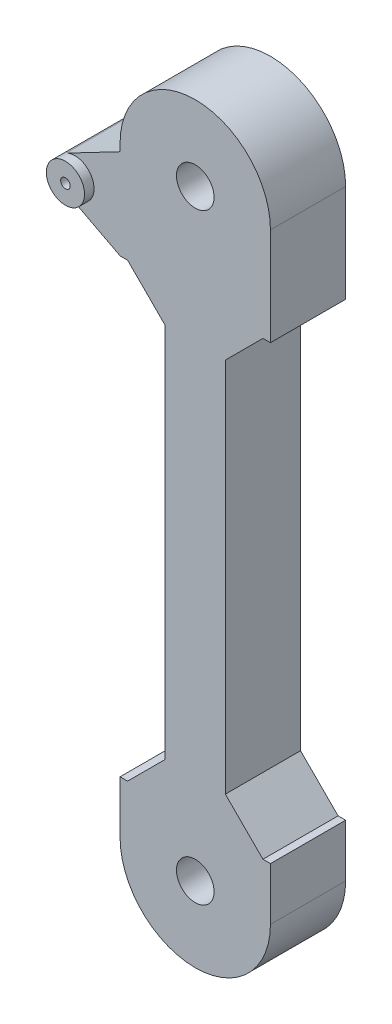
SolidWorks part; units mm, degrees
ref_plane "Front Plane" through (0, 0, 0) normal (0, 0, 1) x (1, 0, 0)
ref_plane "Top Plane" through (0, 0, 0) normal (0, 1, 0) x (1, 0, 0)
ref_plane "Right Plane" through (0, 0, 0) normal (1, 0, 0) x (0, 0, -1)
sketch "Sketch1" plane through (0, 0, 0) normal (0, 0, 1) x (1, 0, 0)
  line L0 (0, 0) -> (0, 80) construction
  line L1 (-10, 80) -> (-10, 0)
  line L2 (10, 0) -> (10, 80)
  arc A0 (-10, 0) -> (10, 0) centre (0, 0) ccw
  arc A1 (10, 80) -> (-10, 80) centre (0, 80) ccw
  point P1 (-12.5, 88.6091)
  point P3 (12.5, 0)
  point P9 (10, 0)
  point P10 (0, 0)
  point P11 (-10, 0)
  dimension "D3" = 20
  dimension "D1" = 80
extrude "Boss-Extrude1" add sketch "Sketch1" along normal blind 10
sketch "Sketch2" plane through (0, 0, 10) normal (0, 0, 1) x (1, 0, 0)
  circle A0 centre (0, 0) radius 2.5
  circle A1 centre (0, 80) radius 2.5
  arc A2 (10, 80) -> (-10, 80) centre (0, 80) ccw construction
  dimension "D1" = 5
  dimension "D2" = 5
extrude "Cut-Extrude1" cut sketch "Sketch2" against normal through all
sketch "Sketch3" plane through (0, 0, 10) normal (0, 0, 1) x (1, 0, 0)
  line L0 (-10, 79) -> (-17.1761, 75.2513)
  line L1 (-10, 80) -> (-10, 0) construction
  line L2 (-17.1761, 70.7487) -> (-10, 67)
  line L3 (-10, 67) -> (-10, 79)
  arc A0 (-17.1761, 75.2513) -> (-17.1761, 70.7487) centre (-16, 73) ccw
  circle A2 centre (0, 80) radius 2.5 construction
  point P9 (-69.7082, 89.3217)
  dimension "D1" = 2.54
  dimension "D2" = 6
  dimension "D3" = 12
  dimension "D4" = 7
extrude "Boss-Extrude2" add sketch "Sketch3" against normal blind 10
sketch "Sketch4" plane through (0, 0, 10) normal (0, 0, 1) x (1, 0, 0)
  circle A0 centre (-16, 73) radius 0.635
  arc A1 (-17.1761, 75.2513) -> (-17.1761, 70.7487) centre (-16, 73) ccw construction
  point P3 (0, 0)
  dimension "D1" = 1.27
extrude "Cut-Extrude2" cut sketch "Sketch4" against normal through all
sketch "Sketch5" plane through (0, 0, 10) normal (0, 0, 1) x (1, 0, 0)
  circle A0 centre (-16, 73) radius 2.54
  circle A1 centre (-16, 73) radius 0.635
  dimension "D1" = 5.08
  dimension "D2" = 1.27
extrude "Boss-Extrude3" add sketch "Sketch5" along normal blind 1.27
sketch "Sketch6" plane through (0, 0, 10) normal (0, 0, 1) x (1, 0, 0)
  line L1 (-10, 67) -> (-4, 67)
  line L2 (-10, 67) -> (-10, 7)
  line L3 (-10, 7) -> (-4, 7)
  line L4 (-4, 67) -> (-4, 7)
  line L9 (0, -6.1985) -> (0, 6.1985) construction
  line L10 (10, 7) -> (4, 7)
  line L11 (4, 67) -> (4, 7)
  line L12 (10, 67) -> (4, 67)
  line L13 (10, 67) -> (10, 7)
  dimension "D1" = 60
  dimension "D2" = 6
extrude "Cut-Extrude3" cut sketch "Sketch6" against normal through all both
chamfer "Chamfer1" distance 5 angle 45 4 edges at (4, 7, 5) (-4, 7, 5) (-4, 67, 5) (4, 67, 5)
